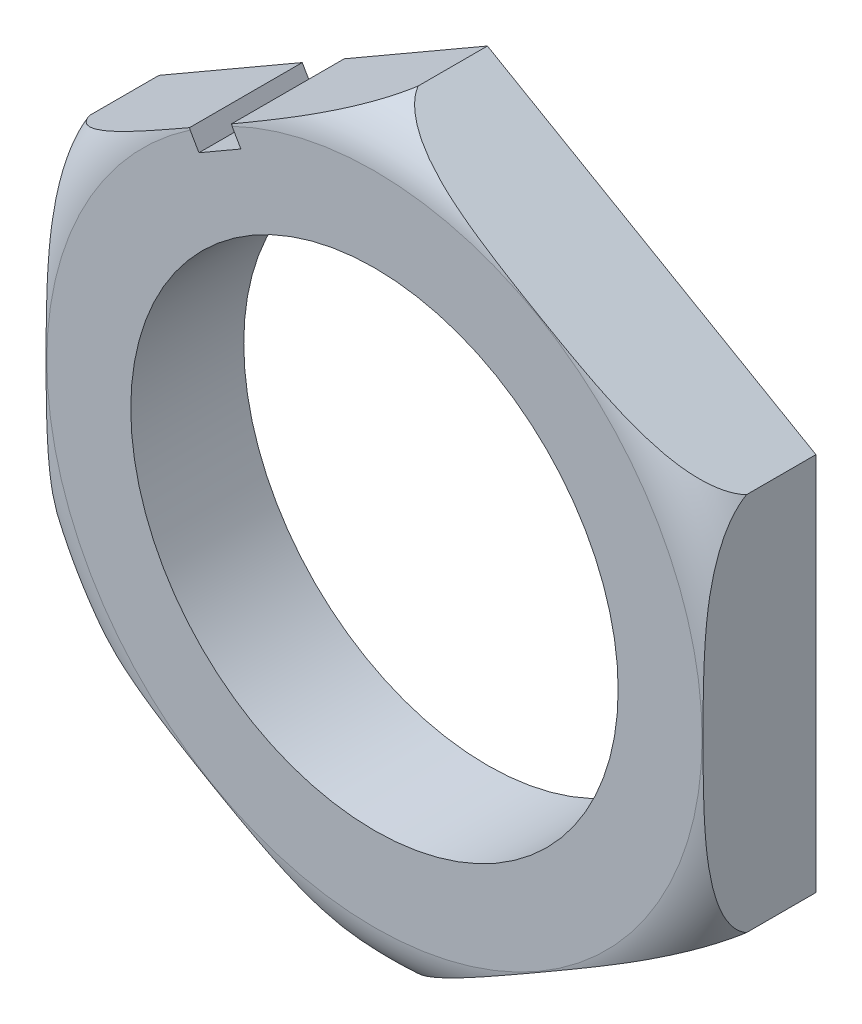
SolidWorks part; units mm, degrees
ref_plane "Спереди" through (0, 0, 0) normal (0, 0, 1) x (1, 0, 0)
ref_plane "Сверху" through (0, 0, 0) normal (0, 1, 0) x (1, 0, 0)
ref_plane "Справа" through (0, 0, 0) normal (1, 0, 0) x (0, 0, -1)
sketch "Эскиз1" plane through (0, 0, 0) normal (0, 0, 1) x (1, 0, 0)
  line L0 (0, 0) -> (0, 23.4538) construction
  line L1 (0, 11.75) -> (-10.1758, 5.875)
  line L2 (-10.1758, 5.875) -> (-10.1758, -5.875)
  line L3 (-10.1758, -5.875) -> (0, -11.75)
  line L4 (0, -11.75) -> (10.1758, -5.875)
  line L5 (10.1758, -5.875) -> (10.1758, 5.875)
  line L6 (10.1758, 5.875) -> (0, 11.75)
  circle A0 centre (0, 0) radius 11.75 construction
  circle A1 centre (0, 0) radius 10.1758 construction
  circle A2 centre (0, 0) radius 7.55
  dimension "D1" = 23.5
  dimension "D3" = 15.1
  dimension "D2" = 11.75
extrude "Бобышка-Вытянуть1" add sketch "Эскиз1" along normal blind 3.5
sketch "Эскиз3" plane through (0, 0, 0) normal (1, 0, 0) x (0, 0, -1)
  line L0 (-10.3495, 0) -> (9.3679, 0) construction
  line L1 (-2.1493, 11.75) -> (-3.5, 11.75)
  line L2 (-3.5, 11.75) -> (0, 11.75) construction
  line L3 (-3.5, 11.75) -> (-3.5, 10.15)
  line L4 (-3.5, 5.875) -> (-3.5, 11.75) construction
  arc A0 (-3.5, 10.15) -> (-2.1493, 11.75) centre (-1.6425, 9.952) cw
  dimension "D3" = 1.868
  dimension "D1" = 1.6
  dimension "D2" = 1.3507
revolve "Вырез-Повернуть2" cut sketch "Эскиз3" angle 360 about L0
ref_plane "Плоскость1" through (0, 0, 20) normal (0, 0, 1) x (1, 0, 0)
sketch "Эскиз4" plane through (0, 0, 20) normal (0, 0, 1) x (1, 0, 0)
  line L0 (-5.0879, 8.8125) -> (5.075, -8.7902) construction
  line L1 (0, 11.75) -> (-10.1758, 5.875) construction
  line L2 (-4.4384, 9.1875) -> (-5.7374, 8.4375)
  line L3 (-5.7374, 8.4375) -> (-5.4374, 7.9179)
  line L4 (-4.4384, 9.1875) -> (-4.1384, 8.6679)
  line L5 (-5.4374, 7.9179) -> (-4.1384, 8.6679)
  circle A0 centre (0, 0) radius 10.15 construction
  dimension "D1" = 0.75
  dimension "D2" = 0.6
extrude "Вырез-Вытянуть1" cut sketch "Эскиз4" against normal blind 27.5
